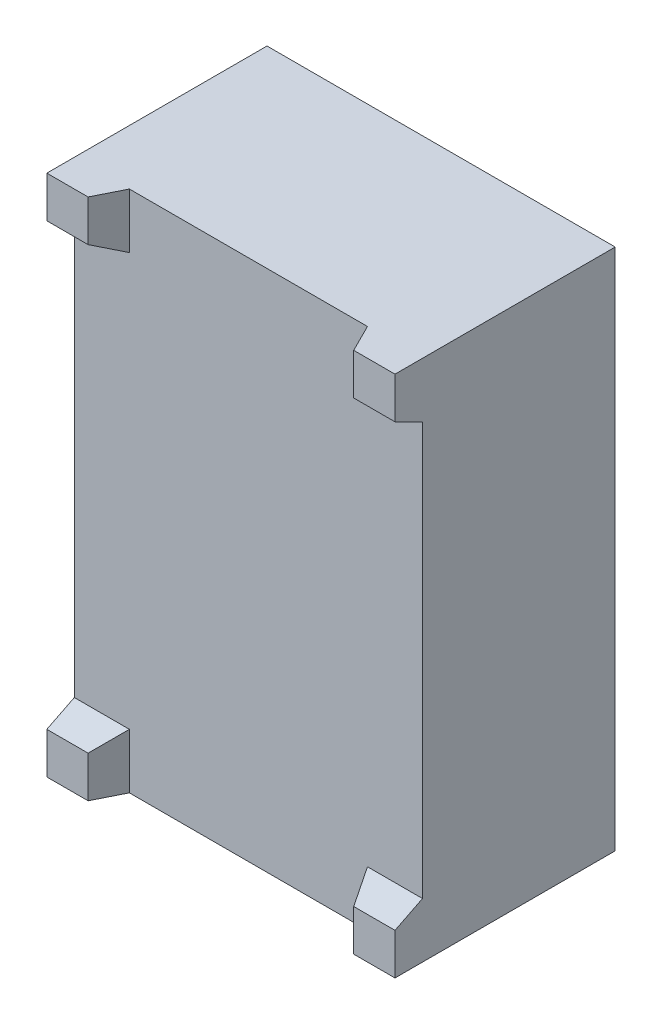
SolidWorks part; units mm, degrees
ref_plane "Ön Düzlem" through (0, 0, 0) normal (0, 0, 1) x (1, 0, 0)
ref_plane "Üst Düzlem" through (0, 0, 0) normal (0, 1, 0) x (1, 0, 0)
ref_plane "Sağ Düzlem" through (0, 0, 0) normal (1, 0, 0) x (0, 0, -1)
sketch "Çizim1" plane through (0, 0, 0) normal (0, 0, 1) x (1, 0, 0)
  line L1 (-6.325, -9.5) -> (6.325, -9.5)
  line L2 (-6.325, -9.5) -> (-6.325, 9.5)
  line L3 (-6.325, 9.5) -> (6.325, 9.5)
  line L4 (6.325, -9.5) -> (6.325, 9.5)
  line L5 (-6.325, -9.5) -> (6.325, 9.5) construction
  line L6 (-6.325, 9.5) -> (6.325, -9.5) construction
  point P0 (0, 0)
  dimension "D1" = 12.65
  dimension "D2" = 19
extrude "Yükseklik-Ekstrüzyon1" add sketch "Çizim1" along normal blind 7.75
sketch "Çizim2" plane through (0, 9.5, 0) normal (0, 1, 0) x (1, 0, 0)
  line L0 (-4.825, -7.75) -> (-4.325, -6.75)
  line L1 (6.325, -7.75) -> (-6.325, -7.75) construction
  line L2 (4.825, -7.75) -> (4.325, -6.75)
  line L3 (6.325, -7.75) -> (6.325, 0) construction
  line L5 (-6.325, -7.75) -> (-6.325, 0) construction
  line L6 (4.325, -6.75) -> (-4.325, -6.75)
  dimension "D1" = 1
  dimension "D2" = 1.5
  dimension "D3" = 2
  dimension "D4" = 2
  dimension "D5" = 1
  dimension "D6" = 1.5
extrude "Kes-Ekstrüzyon1" cut sketch "Çizim2" against normal through all
sketch "Çizim3" plane through (-6.325, 0, 0) normal (-1, 0, 0) x (0, 0, 1)
  line L0 (7.75, 8) -> (6.75, 7.5)
  line L1 (7.75, 9.5) -> (7.75, -9.5) construction
  line L2 (6.75, 7.5) -> (6.75, -7.5)
  line L3 (6.75, -7.5) -> (7.75, -8)
  line L4 (7.75, 9.5) -> (0, 9.5) construction
  line L5 (7.75, -9.5) -> (0, -9.5) construction
  line L6 (7.75, 8) -> (7.75, -8)
  dimension "D1" = 1
  dimension "D2" = 1.5
  dimension "D3" = 2
  dimension "D4" = 1.5
  dimension "D5" = 2
extrude "Kes-Ekstrüzyon2" cut sketch "Çizim3" against normal through all
sketch "Çizim4" plane through (0, 0, 0) normal (0, 0, -1) x (-1, 0, 0)
  line L1 (-6.175, -9.3414) -> (6.175, -9.3414)
  line L2 (-6.175, -9.3414) -> (-6.175, 9.3586)
  line L3 (-6.175, 9.3586) -> (6.175, 9.3586)
  line L4 (6.175, -9.3414) -> (6.175, 9.3586)
  line L8 (5.0079, 5.7142) -> (4.2467, 0.5)
  line L9 (4.0184, 6.8586) -> (3.675, 6.8586)
  line L10 (3.675, 6.8586) -> (2.8783, 1.4016)
  line L11 (1.675, -6.8414) -> (2.3104, -6.8414)
  line L13 (2.8783, 1.4016) -> (3.7467, 0.5)
  line L14 (3.7467, 0.5) -> (4.2467, 0.5)
  line L15 (3.6007, -0.5) -> (4.1007, -0.5)
  line L16 (3.6007, -0.5) -> (2.4913, -1.25)
  line L17 (2.4913, -1.25) -> (1.675, -6.8414)
  line L18 (4.1007, -0.5) -> (3.2999, -5.9858)
  line L19 (-3.2999, 6.0031) -> (-4.1033, 0.5)
  line L20 (-4.1033, 0.5) -> (-3.6033, 0.5)
  line L21 (-3.6033, 0.5) -> (-2.5066, 1.1619)
  line L22 (-2.5066, 1.1619) -> (-1.675, 6.8586)
  line L23 (-1.675, 6.8586) -> (-2.3104, 6.8586)
  line L24 (-5.0079, -5.6969) -> (-4.2493, -0.5)
  line L25 (-4.2493, -0.5) -> (-3.7493, -0.5)
  line L26 (-3.7493, -0.5) -> (-2.8587, -1.25)
  line L27 (-2.8587, -1.25) -> (-3.675, -6.8414)
  line L28 (-3.675, -6.8414) -> (-4.0184, -6.8414)
  line L29 (-3.072, -5.3414) -> (-3.291, -6.8414)
  line L30 (-2.5066, 0.75) -> (2.8783, 0.75)
  line L31 (-2.5066, 0.75) -> (-3.7493, 0)
  line L32 (-3.072, -5.3414) -> (1.51, -5.3414)
  line L33 (-2.8587, -0.75) -> (2.4913, -0.75)
  line L34 (-3.7493, 0) -> (-2.8587, -0.75)
  line L35 (2.8783, 0.75) -> (3.6007, 0)
  line L36 (3.6007, 0) -> (2.4913, -0.75)
  line L37 (1.51, -5.3414) -> (1.291, -6.8414)
  line L38 (-3.291, -6.8414) -> (1.291, -6.8414)
  line L39 (-1.291, 6.8586) -> (-1.51, 5.3586)
  line L40 (-1.291, 6.8586) -> (3.291, 6.8586)
  line L42 (-1.51, 5.3586) -> (3.072, 5.3586)
  line L43 (-6.325, -9.5) -> (-6.325, 9.5) construction
  line L44 (3.291, 6.8586) -> (3.072, 5.3586)
  line L45 (6.325, -9.5) -> (-6.325, -9.5) construction
  arc A0 (5.0079, 5.7142) -> (4.0184, 6.8586) centre (4.0184, 5.8586) ccw
  arc A1 (2.3104, -6.8414) -> (3.2999, -5.9858) centre (2.3104, -5.8414) ccw
  arc A2 (-2.3104, 6.8586) -> (-3.2999, 6.0031) centre (-2.3104, 5.8586) ccw
  arc A3 (-5.0079, -5.6969) -> (-4.0184, -6.8414) centre (-4.0184, -5.8414) ccw
  circle A4 centre (4.975, -6.0914) radius 0.75
  point P0 (0, 0)
  point P20 (0, 0)
  point P21 (0, 0)
  point P66 (0, 0)
  point P67 (0, 0)
  dimension "D12" = 3.253
  dimension "D17" = 0.1586
  dimension "D8" = 2.5757
  dimension "D1" = 1.5
  dimension "D2" = 1
  dimension "D4" = 0.15
  dimension "D5" = 1.3171
  dimension "D6" = 2.0757
  dimension "D7" = 2.2217
  dimension "D9" = 2.65
  dimension "D10" = 3.0251
  dimension "D11" = 3.034
  dimension "D13" = 3.4663
  dimension "D14" = 3.8184
  dimension "D15" = 7.616
  dimension "D16" = 8
  dimension "D18" = 2.6586
  dimension "D34" = 18.8586
  dimension "D36" = 11.3
  dimension "D37" = 19
  dimension "D39" = 12.65
  dimension "D40" = 12.5
extrude "Yükseklik-Ekstrüzyon2" add sketch "Çizim4" along normal blind 0.25 separate body
sketch "Çizim5" plane through (0, 0, -0.25) normal (0, 0, -1) x (-1, 0, 0)
  line L0 (3.291, 6.8586) -> (-1.291, 6.8586) construction
  line L1 (3.072, 5.3586) -> (3.291, 6.8586) construction
  line L2 (-1.51, 5.3586) -> (3.072, 5.3586) construction
  line L3 (-1.291, 6.8586) -> (-1.51, 5.3586) construction
  line L4 (-2.5066, 1.1619) -> (-1.675, 6.8586) construction
  line L5 (-1.675, 6.8586) -> (-2.3104, 6.8586) construction
  line L6 (-3.2999, 6.0031) -> (-4.1033, 0.5) construction
  line L7 (-3.6033, 0.5) -> (-2.5066, 1.1619) construction
  line L8 (-4.1033, 0.5) -> (-3.6033, 0.5) construction
  line L9 (-2.5066, 0.75) -> (-3.7493, 0) construction
  line L10 (2.8783, 0.75) -> (-2.5066, 0.75) construction
  line L11 (3.6007, 0) -> (2.8783, 0.75) construction
  line L12 (2.4913, -0.75) -> (3.6007, 0) construction
  line L13 (-2.8587, -0.75) -> (2.4913, -0.75) construction
  line L14 (-3.7493, 0) -> (-2.8587, -0.75) construction
  line L15 (-2.8587, -1.25) -> (-3.7493, -0.5) construction
  line L16 (-3.7493, -0.5) -> (-4.2493, -0.5) construction
  line L17 (-4.2493, -0.5) -> (-5.0079, -5.6969) construction
  line L18 (-3.675, -6.8414) -> (-2.8587, -1.25) construction
  line L19 (3.675, 6.8586) -> (2.8783, 1.4016) construction
  line L20 (4.0184, 6.8586) -> (3.675, 6.8586) construction
  line L21 (4.2467, 0.5) -> (5.0079, 5.7142) construction
  line L22 (3.7467, 0.5) -> (4.2467, 0.5) construction
  line L23 (2.8783, 1.4016) -> (3.7467, 0.5) construction
  line L24 (3.6007, -0.5) -> (2.4913, -1.25) construction
  line L25 (4.1007, -0.5) -> (3.6007, -0.5) construction
  line L26 (3.2999, -5.9858) -> (4.1007, -0.5) construction
  line L27 (2.4913, -1.25) -> (1.675, -6.8414) construction
  line L28 (-4.0184, -6.8414) -> (-3.675, -6.8414) construction
  line L29 (-3.072, -5.3414) -> (-3.291, -6.8414) construction
  line L30 (1.51, -5.3414) -> (-3.072, -5.3414) construction
  line L31 (1.291, -6.8414) -> (1.51, -5.3414) construction
  line L32 (-3.291, -6.8414) -> (1.291, -6.8414) construction
  line L33 (1.675, -6.8414) -> (2.3104, -6.8414) construction
  line L34 (3.291, 6.8586) -> (-1.291, 6.8586)
  line L35 (3.072, 5.3586) -> (3.291, 6.8586)
  line L36 (-1.51, 5.3586) -> (3.072, 5.3586)
  line L37 (-1.291, 6.8586) -> (-1.51, 5.3586)
  line L38 (-2.5066, 1.1619) -> (-1.675, 6.8586)
  line L39 (-1.675, 6.8586) -> (-2.3104, 6.8586)
  line L40 (-3.2999, 6.0031) -> (-4.1033, 0.5)
  line L41 (-3.6033, 0.5) -> (-2.5066, 1.1619)
  line L42 (-4.1033, 0.5) -> (-3.6033, 0.5)
  line L43 (-2.5066, 0.75) -> (-3.7493, 0)
  line L44 (2.8783, 0.75) -> (-2.5066, 0.75)
  line L45 (3.6007, 0) -> (2.8783, 0.75)
  line L46 (2.4913, -0.75) -> (3.6007, 0)
  line L47 (-2.8587, -0.75) -> (2.4913, -0.75)
  line L48 (-3.7493, 0) -> (-2.8587, -0.75)
  line L49 (-2.8587, -1.25) -> (-3.7493, -0.5)
  line L50 (-3.7493, -0.5) -> (-4.2493, -0.5)
  line L51 (-4.2493, -0.5) -> (-5.0079, -5.6969)
  line L52 (-3.675, -6.8414) -> (-2.8587, -1.25)
  line L53 (3.675, 6.8586) -> (2.8783, 1.4016)
  line L54 (4.0184, 6.8586) -> (3.675, 6.8586)
  line L55 (4.2467, 0.5) -> (5.0079, 5.7142)
  line L56 (3.7467, 0.5) -> (4.2467, 0.5)
  line L57 (2.8783, 1.4016) -> (3.7467, 0.5)
  line L58 (3.6007, -0.5) -> (2.4913, -1.25)
  line L59 (4.1007, -0.5) -> (3.6007, -0.5)
  line L60 (3.2999, -5.9858) -> (4.1007, -0.5)
  line L61 (2.4913, -1.25) -> (1.675, -6.8414)
  line L62 (-4.0184, -6.8414) -> (-3.675, -6.8414)
  line L63 (-3.072, -5.3414) -> (-3.291, -6.8414)
  line L64 (1.51, -5.3414) -> (-3.072, -5.3414)
  line L65 (1.291, -6.8414) -> (1.51, -5.3414)
  line L66 (-3.291, -6.8414) -> (1.291, -6.8414)
  line L67 (1.675, -6.8414) -> (2.3104, -6.8414)
  arc A0 (-2.3104, 6.8586) -> (-3.2999, 6.0031) centre (-2.3104, 5.8586) ccw construction
  arc A1 (5.0079, 5.7142) -> (4.0184, 6.8586) centre (4.0184, 5.8586) ccw construction
  arc A2 (-5.0079, -5.6969) -> (-4.0184, -6.8414) centre (-4.0184, -5.8414) ccw construction
  arc A3 (2.3104, -6.8414) -> (3.2999, -5.9858) centre (2.3104, -5.8414) ccw construction
  circle A4 centre (4.975, -6.0914) radius 0.75 construction
  arc A5 (-2.3104, 6.8586) -> (-3.2999, 6.0031) centre (-2.3104, 5.8586) ccw
  arc A6 (5.0079, 5.7142) -> (4.0184, 6.8586) centre (4.0184, 5.8586) ccw
  arc A7 (-5.0079, -5.6969) -> (-4.0184, -6.8414) centre (-4.0184, -5.8414) ccw
  arc A8 (2.3104, -6.8414) -> (3.2999, -5.9858) centre (2.3104, -5.8414) ccw
  circle A9 centre (4.975, -6.0914) radius 0.75
extrude "Yükseklik-Ekstrüzyon3" add sketch "Çizim5" against normal up to surface (0.25 mm away) separate body up to face at (0, 0, 0)
sketch "Çizim6" plane through (0, 0, 0) normal (0, 0, -1) x (-1, 0, 0)
  line L4 (-6.325, 9.5) -> (-6.325, -9.5)
  line L5 (-6.325, -9.5) -> (6.325, -9.5)
  line L6 (6.325, -9.5) -> (6.325, 9.5)
  line L7 (6.325, 9.5) -> (-6.325, 9.5)
  line L8 (-6.325, 9.5) -> (-6.325, -9.5)
  line L9 (-6.325, -9.5) -> (6.325, -9.5)
  line L10 (6.325, -9.5) -> (6.325, 9.5)
  line L11 (6.325, 9.5) -> (-6.325, 9.5)
  line L12 (6.175, -9.3414) -> (6.175, 9.3586)
  line L13 (6.175, 9.3586) -> (-6.175, 9.3586)
  line L14 (-6.175, 9.3586) -> (-6.175, -9.3414)
  line L15 (-6.175, -9.3414) -> (6.175, -9.3414)
  line L16 (6.175, -9.3414) -> (6.175, 9.3586)
  line L17 (6.175, 9.3586) -> (-6.175, 9.3586)
  line L18 (-6.175, 9.3586) -> (-6.175, -9.3414)
  line L19 (-6.175, -9.3414) -> (6.175, -9.3414)
  dimension "D1" = 0
  dimension "D2" = 0
extrude "Yükseklik-Ekstrüzyon4" add sketch "Çizim6" along normal through all
